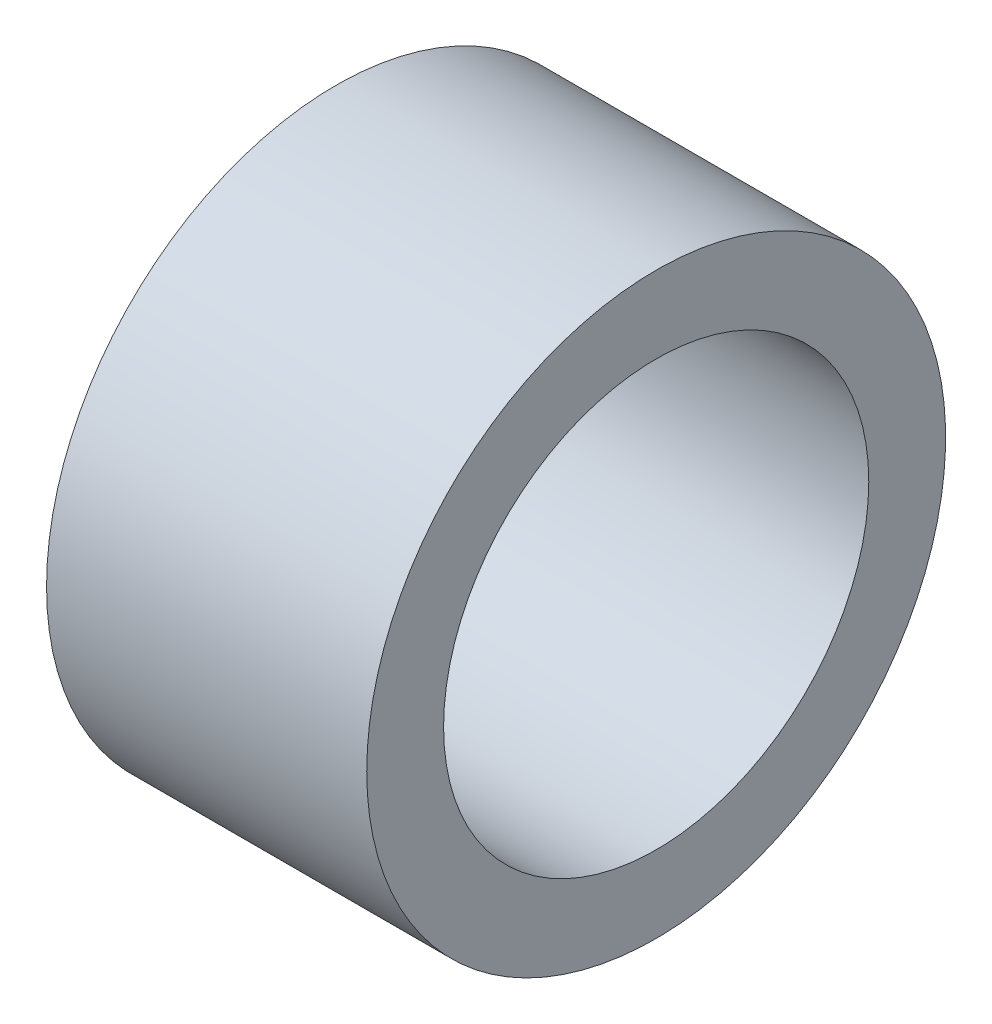
SolidWorks part; units mm, degrees
material "ABS"
ref_plane "Front Plane" through (0, 0, 0) normal (0, 0, 1) x (1, 0, 0)
ref_plane "Top Plane" through (0, 0, 0) normal (0, 1, 0) x (1, 0, 0)
ref_plane "Right Plane" through (0, 0, 0) normal (1, 0, 0) x (0, 0, -1)
sketch "Sketch1" plane through (0, 0, 0) normal (0, 1, 0) x (1, 0, 0)
  line L0 (0, 0) -> (22.4144, 0) construction
  line L1 (0, 0) -> (6.25, 0)
  line L2 (0, 0) -> (0, -4.15)
  line L3 (0, -4.15) -> (6.25, -4.15)
  line L4 (6.25, 0) -> (6.25, -4.15)
  line L5 (0, 0) -> (6.25, 0)
  line L6 (0, 0) -> (0, -5.65)
  line L7 (0, -5.65) -> (6.25, -5.65)
  line L8 (6.25, 0) -> (6.25, -5.65)
  dimension "D1" = 6.25
  dimension "D2" = 4.15
  dimension "D3" = 1.5
revolve "Revolve1" add sketch "Sketch1" angle 360 about L0
